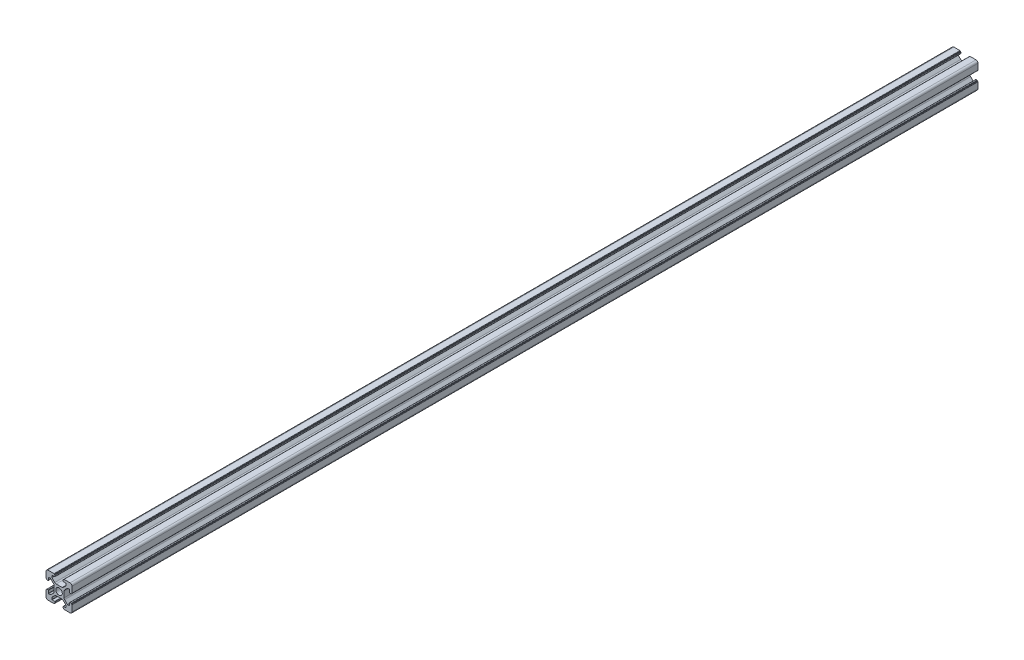
SolidWorks part; units mm, degrees
ref_plane "前视基准面" through (0, 0, 0) normal (0, 0, 1) x (1, 0, 0)
ref_plane "上视基准面" through (0, 0, 0) normal (0, 1, 0) x (1, 0, 0)
ref_plane "右视基准面" through (0, 0, 0) normal (1, 0, 0) x (0, 0, -1)
sketch "草图1" plane through (0, 0, 0) normal (0, 0, 1) x (1, 0, 0)
  line L0 (0, 0) -> (0, 5.5) construction
  line L1 (-8.5023, -10.0023) -> (-3.85, -10.0023)
  line L2 (-10.0023, -8.5023) -> (-10.0023, -3.85)
  line L3 (-8.5023, 10.0023) -> (-3.85, 10.0023)
  line L4 (10.0023, -8.5023) -> (10.0023, -3.85)
  line L5 (-10.0023, -10.0023) -> (10.0023, 10.0023) construction
  line L6 (-10.0023, 10.0023) -> (10.0023, -10.0023) construction
  line L7 (-2.218, -3.9) -> (2.218, -3.9)
  line L8 (-3.9, -2.218) -> (-3.9, 2.218)
  line L9 (-2.218, 3.9) -> (2.218, 3.9)
  line L10 (3.9, -2.218) -> (3.9, 2.218)
  line L11 (-3.9, -3.9) -> (3.9, 3.9) construction
  line L12 (-3.9, 3.9) -> (3.9, -3.9) construction
  line L13 (-5.25, -8.2) -> (-3.35, -8.2)
  line L14 (-8.2, -5.25) -> (-8.2, -3.35)
  line L15 (-5.25, 8.2) -> (-3.35, 8.2)
  line L16 (8.2, -5.25) -> (8.2, -3.35)
  line L17 (-8.2, -8.2) -> (8.2, 8.2) construction
  line L18 (-8.2, 8.2) -> (8.2, -8.2) construction
  line L19 (-7.95, 5.5) -> (-6.6642, 5.5)
  line L20 (0, 0) -> (5.5, 0) construction
  line L23 (-5.5, 7.95) -> (-5.5, 6.6642)
  line L26 (0, 0) -> (-0.5303, 0.5303)
  line L27 (3.2787, 4.3393) -> (5.4268, 6.4874)
  line L28 (0, 0) -> (0.5303, -0.5303)
  line L29 (5.5, 6.6642) -> (5.5, 7.95)
  line L30 (4.3393, 3.2787) -> (6.4874, 5.4268)
  line L31 (6.6642, 5.5) -> (7.95, 5.5)
  line L32 (4.3393, -3.2787) -> (6.4874, -5.4268)
  line L33 (3.2787, -4.3393) -> (5.4268, -6.4874)
  line L34 (-3.2787, -4.3393) -> (-5.4268, -6.4874)
  line L35 (-4.3393, -3.2787) -> (-6.4874, -5.4268)
  line L36 (-4.3393, 3.2787) -> (-6.4874, 5.4268)
  line L37 (-3.2787, 4.3393) -> (-5.4268, 6.4874)
  line L38 (3.1, -8.45) -> (3.1, -9.2523)
  line L39 (8.45, 3.1) -> (9.2523, 3.1)
  line L40 (-5.5, -6.6642) -> (-5.5, -7.95)
  line L41 (-6.6642, -5.5) -> (-7.95, -5.5)
  line L42 (5.5, -6.6642) -> (5.5, -7.95)
  line L43 (6.6642, -5.5) -> (7.95, -5.5)
  line L44 (9.2523, -3.1) -> (8.45, -3.1)
  line L46 (10.0023, 3.85) -> (10.0023, 8.5023)
  line L47 (8.2, 3.35) -> (8.2, 5.25)
  line L48 (-3.1, -9.2523) -> (-3.1, -8.45)
  line L49 (-8.45, -3.1) -> (-9.2523, -3.1)
  line L50 (-9.2523, 3.1) -> (-8.45, 3.1)
  line L51 (-3.1, 8.45) -> (-3.1, 9.2523)
  line L52 (3.1, 9.2523) -> (3.1, 8.45)
  line L53 (3.85, 10.0023) -> (8.5023, 10.0023)
  line L54 (3.35, 8.2) -> (5.25, 8.2)
  line L55 (-10.0023, 3.85) -> (-10.0023, 8.5023)
  line L56 (-8.2, 3.35) -> (-8.2, 5.25)
  line L57 (3.35, -8.2) -> (5.25, -8.2)
  line L58 (3.85, -10.0023) -> (8.5023, -10.0023)
  line L59 (9.7523, -3.6) -> (9.5023, -3.6)
  line L61 (9.7523, 3.6) -> (9.5023, 3.6)
  line L62 (9.5023, -3.6) -> (9.5023, -3.35)
  line L63 (3.6, -9.7523) -> (3.6, -9.5023)
  line L64 (3.35, -9.5023) -> (3.6, -9.5023)
  line L65 (9.5023, 3.35) -> (9.5023, 3.6)
  line L66 (-3.6, -9.5023) -> (-3.35, -9.5023)
  line L67 (-3.6, -9.7523) -> (-3.6, -9.5023)
  line L68 (-9.7523, -3.6) -> (-9.5023, -3.6)
  line L69 (-9.5023, -3.35) -> (-9.5023, -3.6)
  line L70 (-9.5023, 3.6) -> (-9.5023, 3.35)
  line L71 (-9.7523, 3.6) -> (-9.5023, 3.6)
  line L72 (-3.6, 9.7523) -> (-3.6, 9.5023)
  line L73 (-3.35, 9.5023) -> (-3.6, 9.5023)
  line L74 (3.6, 9.5023) -> (3.35, 9.5023)
  line L75 (3.6, 9.7523) -> (3.6, 9.5023)
  circle A0 centre (0, 0) radius 2.5
  arc A1 (10.0023, 8.5023) -> (8.5023, 10.0023) centre (8.5023, 8.5023) ccw
  arc A2 (8.5023, -10.0023) -> (10.0023, -8.5023) centre (8.5023, -8.5023) ccw
  arc A3 (-10.0023, -8.5023) -> (-8.5023, -10.0023) centre (-8.5023, -8.5023) ccw
  arc A4 (-10.0023, 8.5023) -> (-8.5023, 10.0023) centre (-8.5023, 8.5023) cw
  arc A5 (-9.5023, -3.35) -> (-9.2523, -3.1) centre (-9.2523, -3.35) cw
  arc A6 (-9.7523, -3.6) -> (-10.0023, -3.85) centre (-9.7523, -3.85) ccw
  arc A7 (-8.45, -3.1) -> (-8.2, -3.35) centre (-8.45, -3.35) cw
  arc A8 (-7.95, -5.5) -> (-8.2, -5.25) centre (-7.95, -5.25) cw
  arc A9 (-6.4874, -5.4268) -> (-6.6642, -5.5) centre (-6.6642, -5.25) cw
  arc A10 (-5.4268, -6.4874) -> (-5.5, -6.6642) centre (-5.25, -6.6642) ccw
  arc A11 (-5.5, -7.95) -> (-5.25, -8.2) centre (-5.25, -7.95) ccw
  arc A12 (-3.6, -9.7523) -> (-3.85, -10.0023) centre (-3.85, -9.7523) cw
  arc A13 (-3.35, -9.5023) -> (-3.1, -9.2523) centre (-3.35, -9.2523) ccw
  arc A14 (-3.1, -8.45) -> (-3.35, -8.2) centre (-3.35, -8.45) ccw
  arc A15 (3.1, -8.45) -> (3.35, -8.2) centre (3.35, -8.45) cw
  arc A16 (5.5, -7.95) -> (5.25, -8.2) centre (5.25, -7.95) cw
  arc A17 (5.4268, -6.4874) -> (5.5, -6.6642) centre (5.25, -6.6642) cw
  arc A18 (6.4874, -5.4268) -> (6.6642, -5.5) centre (6.6642, -5.25) ccw
  arc A19 (7.95, -5.5) -> (8.2, -5.25) centre (7.95, -5.25) ccw
  arc A20 (8.45, -3.1) -> (8.2, -3.35) centre (8.45, -3.35) ccw
  arc A21 (9.5023, -3.35) -> (9.2523, -3.1) centre (9.2523, -3.35) ccw
  arc A22 (9.7523, -3.6) -> (10.0023, -3.85) centre (9.7523, -3.85) cw
  arc A23 (3.35, -9.5023) -> (3.1, -9.2523) centre (3.35, -9.2523) cw
  arc A24 (3.6, -9.7523) -> (3.85, -10.0023) centre (3.85, -9.7523) ccw
  arc A25 (7.95, 5.5) -> (8.2, 5.25) centre (7.95, 5.25) cw
  arc A26 (8.2, 3.35) -> (8.45, 3.1) centre (8.45, 3.35) ccw
  arc A27 (9.5023, 3.35) -> (9.2523, 3.1) centre (9.2523, 3.35) cw
  arc A28 (9.7523, 3.6) -> (10.0023, 3.85) centre (9.7523, 3.85) ccw
  arc A29 (6.6642, 5.5) -> (6.4874, 5.4268) centre (6.6642, 5.25) ccw
  arc A30 (5.4268, 6.4874) -> (5.5, 6.6642) centre (5.25, 6.6642) ccw
  arc A31 (5.5, 7.95) -> (5.25, 8.2) centre (5.25, 7.95) ccw
  arc A32 (3.1, 8.45) -> (3.35, 8.2) centre (3.35, 8.45) ccw
  arc A33 (3.6, 9.7523) -> (3.85, 10.0023) centre (3.85, 9.7523) cw
  arc A34 (3.35, 9.5023) -> (3.1, 9.2523) centre (3.35, 9.2523) ccw
  arc A35 (-9.7523, 3.6) -> (-10.0023, 3.85) centre (-9.7523, 3.85) cw
  arc A36 (-9.5023, 3.35) -> (-9.2523, 3.1) centre (-9.2523, 3.35) ccw
  arc A37 (-8.45, 3.1) -> (-8.2, 3.35) centre (-8.45, 3.35) ccw
  arc A38 (-8.2, 5.25) -> (-7.95, 5.5) centre (-7.95, 5.25) cw
  arc A39 (-6.4874, 5.4268) -> (-6.6642, 5.5) centre (-6.6642, 5.25) ccw
  arc A40 (-5.4268, 6.4874) -> (-5.5, 6.6642) centre (-5.25, 6.6642) cw
  arc A41 (-5.5, 7.95) -> (-5.25, 8.2) centre (-5.25, 7.95) cw
  arc A42 (-3.1, 8.45) -> (-3.35, 8.2) centre (-3.35, 8.45) cw
  arc A43 (-3.1, 9.2523) -> (-3.35, 9.5023) centre (-3.35, 9.2523) ccw
  arc A44 (-3.6, 9.7523) -> (-3.85, 10.0023) centre (-3.85, 9.7523) ccw
  arc A45 (-4.3393, 3.2787) -> (-3.9, 2.218) centre (-5.4, 2.218) cw
  arc A46 (-3.2787, 4.3393) -> (-2.218, 3.9) centre (-2.218, 5.4) ccw
  arc A47 (3.2787, 4.3393) -> (2.218, 3.9) centre (2.218, 5.4) cw
  arc A48 (4.3393, 3.2787) -> (3.9, 2.218) centre (5.4, 2.218) ccw
  arc A49 (4.3393, -3.2787) -> (3.9, -2.218) centre (5.4, -2.218) cw
  arc A50 (3.2787, -4.3393) -> (2.218, -3.9) centre (2.218, -5.4) ccw
  arc A51 (-4.3393, -3.2787) -> (-3.9, -2.218) centre (-5.4, -2.218) ccw
  arc A52 (-2.218, -3.9) -> (-3.2787, -4.3393) centre (-2.218, -5.4) ccw
  point P0 (0, 0)
  point P7 (10.0023, 0)
  point P62 (0, 0)
  point P76 (0, 0)
  point P92 (-8.2, -5.5)
  point P99 (0, 0)
  point P106 (-5.5, -8.2)
  point P117 (5.5, -8.2)
  point P124 (8.2, -5.5)
  point P137 (8.2, 5.5)
  point P140 (8.2, 3.1)
  point P147 (6.5607, 5.5)
  point P152 (5.5, 8.2)
  point P167 (-8.2, 5.5)
  point P174 (-5.5, 8.2)
  dimension "D1" = 1.5
  dimension "D5" = 0.25
  dimension "D6" = 1.5
  dimension "D2" = 4
  dimension "D3" = 4
  dimension "D4" = 4
extrude "凸台-拉伸1" add sketch "草图1" along normal blind 1220 contours A52 L7 A50 L33 A17 L42 A16 L57 A15 L38 A23 L64 L63 A24 L58 A2 L4 A22 L59 L62 A21 L44 A20 L16 A19 L43 A18 L32 A49 L10 A48 L30 A29 L31 A25 L47 A26 L39 A27 L65 L61 A28 L46 A1 L53 A33 L75 L74 A34 L52 A32
ref_plane "Plane1" through (0, 0, 524) normal (0, 0, 1) x (1, 0, 0)
sketch "Sketch1" plane through (0, 0, 524) normal (0, 0, 1) x (1, 0, 0)
  circle A0 centre (0, 0) radius 16.7715
extrude "Cut-Extrude1" cut sketch "Sketch1" against normal through all
ref_plane "CenterPlane" through (0, 0, 872) normal (0, 0, 1) x (1, 0, 0)
